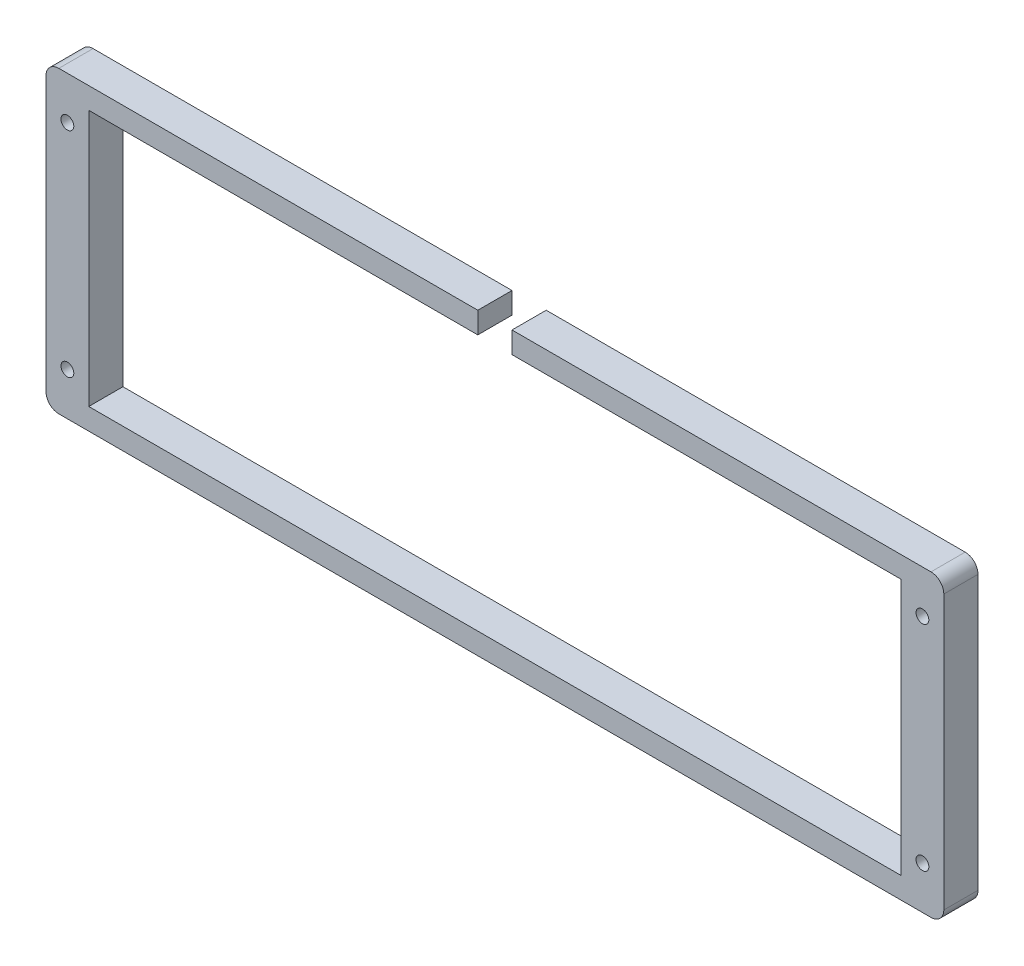
SolidWorks part; units mm, degrees
ref_plane "前视基准面" through (0, 0, 0) normal (0, 0, 1) x (1, 0, 0)
ref_plane "上视基准面" through (0, 0, 0) normal (0, 1, 0) x (1, 0, 0)
ref_plane "右视基准面" through (0, 0, 0) normal (1, 0, 0) x (0, 0, -1)
sketch "草图1" plane through (0, 0, 0) normal (0, 0, 1) x (1, 0, 0)
  line L1 (-30, 46.5) -> (180, 46.5)
  line L2 (-30, 46.5) -> (-30, -23.5)
  line L3 (-30, -23.5) -> (180, -23.5)
  line L5 (180, 46.5) -> (180, -23.5)
  dimension "D1" = 210
  dimension "D2" = 70
  dimension "D3" = 46.5
  dimension "D4" = 30
extrude "凸台-拉伸1" add sketch "草图1" along normal blind 8
sketch "草图2" plane through (0, 0, 0) normal (0, 0, 1) x (1, 0, 0)
  line L0 (-30, 46.5) -> (-30, -23.5) construction
  line L1 (-20, 41.5) -> (170, 41.5)
  line L2 (-20, 41.5) -> (-20, -18.5)
  line L3 (-20, -18.5) -> (170, -18.5)
  line L4 (170, 41.5) -> (170, -18.5)
  line L5 (180, 46.5) -> (-30, 46.5) construction
  line L6 (180, -23.5) -> (180, 46.5) construction
  line L7 (-30, -23.5) -> (180, -23.5) construction
  dimension "D1" = 10
  dimension "D2" = 5
  dimension "D3" = 10
  dimension "D4" = 5
extrude "切除-拉伸1" cut sketch "草图2" along normal blind 10
sketch "草图3" plane through (0, 0, 0) normal (0, 0, 1) x (1, 0, 0)
  line L0 (-30, 46.5) -> (-30, -23.5) construction
  line L4 (180, -23.5) -> (180, 46.5) construction
  line L6 (-30, -23.5) -> (180, -23.5) construction
  line L9 (180, 46.5) -> (-30, 46.5) construction
  circle A0 centre (-25, 36.5) radius 1.5
  circle A1 centre (175, 36.5) radius 1.5
  circle A2 centre (-25, -13.5) radius 1.5
  circle A3 centre (175, -13.5) radius 1.5
  dimension "D1" = 3
  dimension "D3" = 10
  dimension "D4" = 5
  dimension "D5" = 10
  dimension "D6" = 3
  dimension "D7" = 3
  dimension "D8" = 5
  dimension "D9" = 10
  dimension "D10" = 5
  dimension "D11" = 3
  dimension "D12" = 10
  dimension "D2" = 5
extrude "切除-拉伸2" cut sketch "草图3" along normal blind 10
sketch "草图4" plane through (0, 46.5, 0) normal (0, 1, 0) x (1, 0, 0)
  line L0 (75, -8) -> (75, 0) construction
  line L1 (180, -8) -> (-30, -8) construction
  line L2 (180, 0) -> (-30, 0) construction
  line L4 (71, -10) -> (79, -10)
  line L5 (71, -10) -> (71, 0)
  line L6 (71, 0) -> (79, 0)
  line L7 (79, -10) -> (79, 0)
  line L8 (71, -10) -> (79, 0) construction
  line L9 (71, 0) -> (79, -10) construction
  point P6 (75, -5)
  dimension "D2" = 8
  dimension "D3" = 10
extrude "切除-拉伸3" cut sketch "草图4" against normal blind 5
fillet "圆角1" radius 3 4 edges at (180, -23.5, 4) (180, 46.5, 4) (-30, -23.5, 4) (-30, 46.5, 4)
